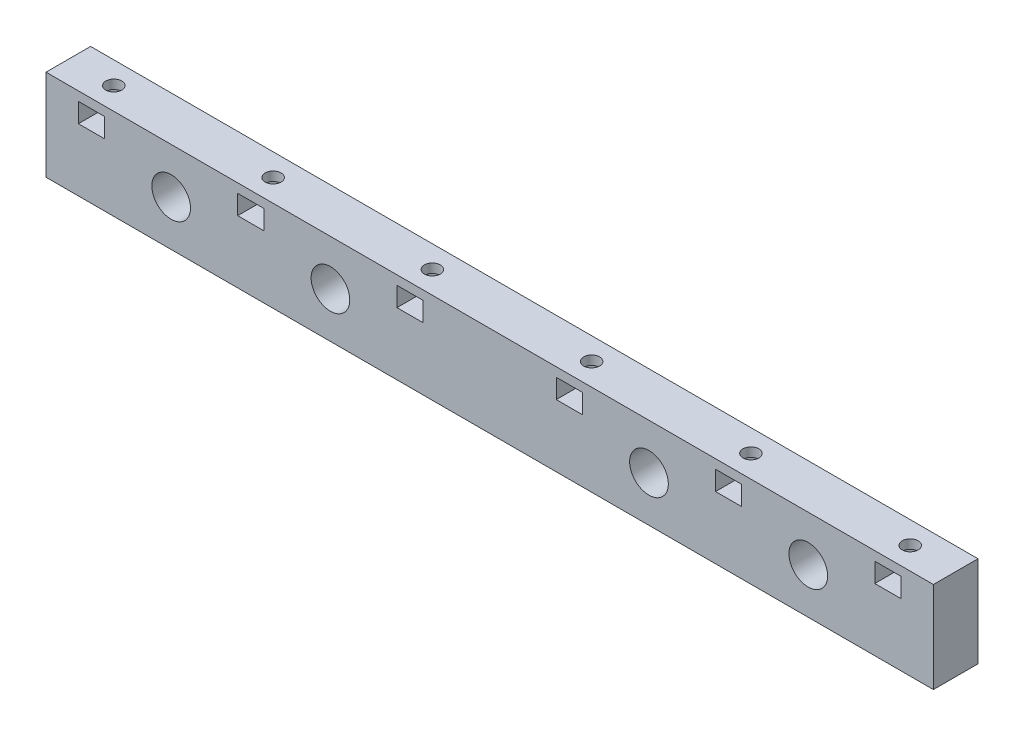
SolidWorks part; units mm, degrees
ref_plane "Front Plane" through (0, 0, 0) normal (0, 0, 1) x (1, 0, 0)
ref_plane "Top Plane" through (0, 0, 0) normal (0, 1, 0) x (1, 0, 0)
ref_plane "Right Plane" through (0, 0, 0) normal (1, 0, 0) x (0, 0, -1)
sketch "Sketch1" plane through (0, 0, 0) normal (0, 0, 1) x (1, 0, 0)
  line L1 (-97.5, -10) -> (97.5, -10)
  line L2 (-97.5, -10) -> (-97.5, 10)
  line L3 (-97.5, 10) -> (97.5, 10)
  line L4 (97.5, -10) -> (97.5, 10)
  line L5 (-97.5, -10) -> (97.5, 10) construction
  line L6 (-97.5, 10) -> (97.5, -10) construction
  point P0 (0, 0)
  dimension "D1" = 20
  dimension "D2" = 195
extrude "Boss-Extrude1" add sketch "Sketch1" along normal mid plane 9.8
sketch "Sketch2" plane through (0, 10, 0) normal (0, 1, 0) x (1, 0, 0)
  line L0 (-97.5, -4.9) -> (-97.5, 4.9) construction
  circle A0 centre (-87.5, 0) radius 1.75
  dimension "D1" = 3.5
  dimension "D2" = 10
extrude "Cut-Extrude1" cut sketch "Sketch2" against normal blind 6
sketch "Sketch3" plane through (0, 10, 0) normal (0, 1, 0) x (1, 0, 0)
  line L1 (-87.5, 3.3198) -> (-90.375, 1.6599)
  line L2 (-90.375, 1.6599) -> (-90.375, -1.6599)
  line L3 (-90.375, -1.6599) -> (-87.5, -3.3198)
  line L4 (-87.5, -3.3198) -> (-84.625, -1.6599)
  line L5 (-84.625, -1.6599) -> (-84.625, 1.6599)
  line L6 (-84.625, 1.6599) -> (-87.5, 3.3198)
  circle A0 centre (-87.5, 0) radius 2.875 construction
  dimension "D1" = 5.75
extrude "Cut-Extrude2" cut sketch "Sketch3" against normal blind 4.25 from offset 2 offset against normal yes
sketch "Sketch4" plane through (0, 0, 0) normal (0, 0, 1) x (1, 0, 0)
  line L0 (-90.375, 3.75) -> (-90.375, 8) construction
  line L1 (-90.375, 8) -> (-84.625, 8)
  line L2 (-90.375, 8) -> (-90.375, 3.75)
  line L3 (-90.375, 3.75) -> (-84.625, 3.75)
  line L4 (-84.625, 8) -> (-84.625, 3.75)
  line L6 (-84.625, 3.75) -> (-84.625, 8) construction
  line L7 (-89.25, 8) -> (-85.75, 8) construction
  line L8 (-84.625, 3.75) -> (-87.5, 3.75) construction
extrude "Cut-Extrude3" cut sketch "Sketch4" along normal through all
pattern_linear "LPattern1" count 3 spacing 35 along (1, 0, 0) of "Cut-Extrude1", "Cut-Extrude2", "Cut-Extrude3"
mirror "Mirror1" about plane through (0, 0, 0) normal (1, 0, 0) of "LPattern1", "Cut-Extrude1", "Cut-Extrude2", "Cut-Extrude3"
sketch "Sketch5" plane through (0, 0, 4.9) normal (0, 0, 1) x (1, 0, 0)
  line L1 (-87.5, 5.875) -> (-52.5, 5.875) construction
  line L2 (-87.5, 3.75) -> (-87.5, 8) construction
  line L3 (-52.5, 3.75) -> (-52.5, 8) construction
  circle A0 centre (-70, 0) radius 4.25
  point P4 (-70, 5.875)
  dimension "D1" = 8.5
extrude "Cut-Extrude4" cut sketch "Sketch5" against normal blind 6
sketch "Sketch6" plane through (0, 0, -1.1) normal (0, 0, 1) x (1, 0, 0)
  circle A0 centre (-70, 0) radius 2.625
  circle A1 centre (-70, 0) radius 4.25 construction
  dimension "D1" = 5.25
extrude "Cut-Extrude5" cut sketch "Sketch6" against normal through all both and the other way through all
pattern_linear "LPattern2" count 2 spacing 35 along (1, 0, 0) of "Cut-Extrude5", "Cut-Extrude4"
mirror "Mirror2" about plane through (0, 0, 0) normal (1, 0, 0) of "LPattern2", "Cut-Extrude4", "Cut-Extrude5"
sketch "Sketch7" [suppressed] plane through (0, 0, 4.9) normal (0, 0, 1) x (1, 0, 0)
  line L0 (-87.5, 8.575) -> (-52.5, 8.575) construction
  line L1 (-87.5, 6.45) -> (-87.5, 10.7) construction
  line L2 (-52.5, 6.45) -> (-52.5, 10.7) construction
  circle A0 centre (-70, 0) radius 2.625
  point P8 (-70, 8.575)
  dimension "D1" = 5.25
extrude "Cut-Extrude6" [suppressed] cut sketch "Sketch7" against normal through all both and the other way through all
sketch "Sketch8" [suppressed] plane through (0, 0, 4.9) normal (0, 0, 1) x (1, 0, 0)
  line L1 (-70, 4.6188) -> (-74, 2.3094)
  line L2 (-74, 2.3094) -> (-74, -2.3094)
  line L3 (-74, -2.3094) -> (-70, -4.6188)
  line L4 (-70, -4.6188) -> (-66, -2.3094)
  line L5 (-66, -2.3094) -> (-66, 2.3094)
  line L6 (-66, 2.3094) -> (-70, 4.6188)
  circle A0 centre (-70, 0) radius 4 construction
  dimension "D1" = 8
extrude "Cut-Extrude7" [suppressed] cut sketch "Sketch8" against normal blind 5 and the other way through all
pattern_linear "LPattern3" [suppressed] count 2 spacing 35
mirror "Mirror3" [suppressed] about plane through (0, 0, 0) normal (1, 0, 0)
